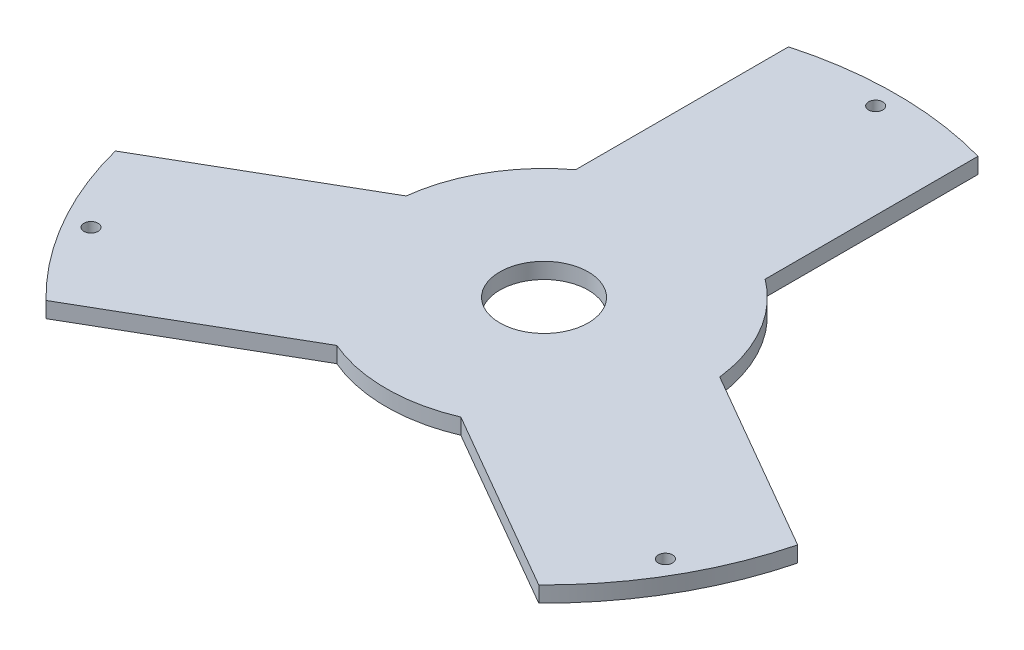
SolidWorks part; units mm, degrees
ref_plane "Front Plane" through (0, 0, 0) normal (0, 0, 1) x (1, 0, 0)
ref_plane "Top Plane" through (0, 0, 0) normal (0, 1, 0) x (1, 0, 0)
ref_plane "Right Plane" through (0, 0, 0) normal (1, 0, 0) x (0, 0, -1)
sketch "Sketch2" plane through (0, 0, 0) normal (0, 1, 0) x (1, 0, 0)
  circle A0 centre (0, 0) radius 111.5
  circle A1 centre (0, 0) radius 14
  dimension "D1" = 223
  dimension "D2" = 28
extrude "Boss-Extrude1" add sketch "Sketch2" along normal blind 5
sketch "Sketch5" plane through (0, 5, 0) normal (0, 1, 0) x (1, 0, 0)
  circle A0 centre (0, 105) radius 2.6 construction
  circle A1 centre (90.9327, -52.5) radius 2.6 construction
  circle A2 centre (-90.9327, -52.5) radius 2.6 construction
  circle A3 centre (0, 105) radius 2.6
  circle A4 centre (90.9327, -52.5) radius 2.6
  circle A5 centre (-90.9327, -52.5) radius 2.6
hole_wizard "M4 Clearance Hole2" positions "Sketch6" profile "Sketch7" hole size "M4" standard "ISO" end condition through all
sketch "Sketch6" plane through (0, 5, 0) normal (0, 1, 0) x (1, 0, 0)
  circle A2 centre (-90.9327, -52.5) radius 2.6
  circle A3 centre (-90.9327, -52.5) radius 2.6
  circle A6 centre (90.9327, -52.5) radius 2.6
  circle A7 centre (90.9327, -52.5) radius 2.6
  circle A10 centre (0, 105) radius 2.6
  circle A11 centre (0, 105) radius 2.6
  point P5 (-90.9327, -52.5)
  point P12 (90.9327, -52.5)
  point P19 (0, 105)
  dimension "D1" = 0
  dimension "D2" = 0
  dimension "D3" = 0
sketch "Sketch7" plane through (-90.9327, 5, 52.5) normal (1, 0, 0) x (0, 0, 1)
  line L0 (0, 0) -> (0, 5)
  line L1 (0, 5) -> (2.25, 5)
  line L2 (2.25, 5) -> (2.25, 0)
  line L5 (2.25, 0) -> (0, 0)
  line L11 (0, -6.35) -> (0, 107.95) construction
  dimension "Thru Hole Dia." = 4.5
  dimension "Thru Hole Depth" = 5
sketch "Sketch8" plane through (0, 5, 0) normal (0, 1, 0) x (1, 0, 0)
  line L0 (0, 0) -> (0, 97.97) construction
  line L1 (-30, 40) -> (-30, 107.3883)
  line L2 (30, 40) -> (30, 107.3883)
  line L3 (49.641, 5.9808) -> (108.001, -27.7134)
  line L4 (19.641, -45.9808) -> (78.001, -79.6749)
  line L5 (-19.641, -45.9808) -> (-78.001, -79.6749)
  line L6 (-49.641, 5.9808) -> (-108.001, -27.7134)
  arc A0 (-19.641, -45.9808) -> (19.641, -45.9808) centre (0, 0) ccw
  circle A1 centre (0, 0) radius 111.5
  arc A2 (-78.001, -79.6749) -> (78.001, -79.6749) centre (0, 0) ccw
  arc A3 (49.641, 5.9808) -> (30, 40) centre (0, 0) ccw
  arc A4 (-30, 40) -> (-49.641, 5.9808) centre (0, 0) ccw
  arc A5 (-30, 107.3883) -> (-108.001, -27.7134) centre (0, 0) ccw
  arc A6 (108.001, -27.7134) -> (30, 107.3883) centre (0, 0) ccw
  point P10 (0, 0)
  point P20 (0, 0)
  dimension "D2" = 100
  dimension "D3" = 60
  dimension "D1" = 0
  dimension "D4" = 3
extrude "Cut-Extrude1" cut sketch "Sketch8" against normal through all
